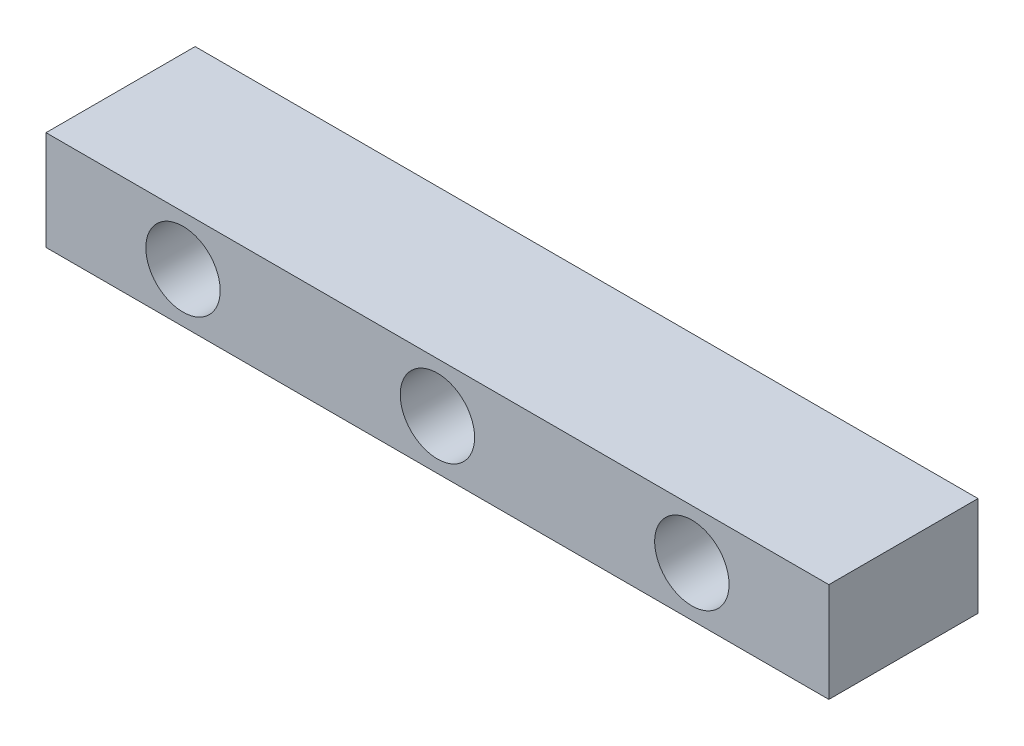
SolidWorks part; units mm, degrees
ref_plane "Front Plane" through (0, 0, 0) normal (0, 0, 1) x (1, 0, 0)
ref_plane "Top Plane" through (0, 0, 0) normal (0, 1, 0) x (1, 0, 0)
ref_plane "Right Plane" through (0, 0, 0) normal (1, 0, 0) x (0, 0, -1)
sketch "Sketch1" plane through (0, 0, 0) normal (0, 1, 0) x (1, 0, 0)
  line L1 (0, 0) -> (400, 0)
  line L2 (0, 0) -> (0, 76.2)
  line L3 (0, 76.2) -> (400, 76.2)
  line L4 (400, 0) -> (400, 76.2)
  dimension "D1" = 400
  dimension "D2" = 76.2
extrude "Boss-Extrude1" add sketch "Sketch1" along normal blind 50.8
sketch "Sketch2" plane through (0, 0, 0) normal (0, 0, 1) x (1, 0, 0)
  line L0 (70, 25.4) -> (200, 25.4)
  line L1 (0, 0) -> (70, 0)
  line L2 (0, 0) -> (0, 25.4)
  line L3 (0, 25.4) -> (70, 25.4)
  line L4 (70, 0) -> (70, 25.4)
  line L5 (200, 25.4) -> (330, 25.4)
  circle A0 centre (70, 25.4) radius 19
  circle A1 centre (200, 25.4) radius 19
  circle A2 centre (330, 25.4) radius 19
  dimension "D1" = 70
  dimension "D2" = 25.4
  dimension "D3" = 130
  dimension "D4" = 130
extrude "Cut-Extrude1" cut sketch "Sketch2" against normal blind 76.2 contours A0 | A1 | A2
